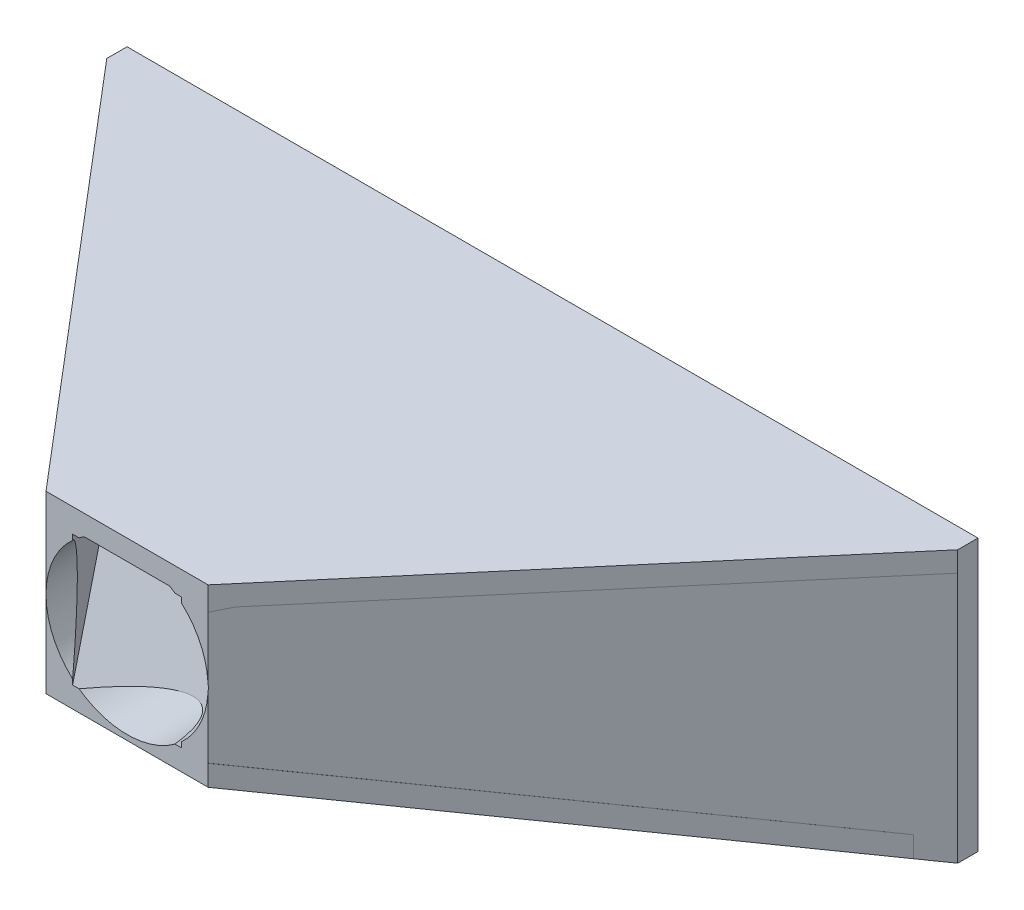
SolidWorks part; units mm, degrees
ref_plane "Plan de face" through (0, 0, 0) normal (0, 0, 1) x (1, 0, 0)
ref_plane "Plan de dessus" through (0, 0, 0) normal (0, 1, 0) x (1, 0, 0)
ref_plane "Plan de droite" through (0, 0, 0) normal (1, 0, 0) x (0, 0, -1)
sketch "Esquisse1" plane through (0, 0, 0) normal (0, 0, 1) x (1, 0, 0)
  line L0 (-5, 18.1802) -> (-5, -71.8198)
  line L1 (0, 13.1802) -> (200, 13.1802)
  line L2 (0, 13.1802) -> (0, -66.8198)
  line L3 (0, -66.8198) -> (200, -66.8198)
  line L4 (200, 13.1802) -> (200, -66.8198)
  line L5 (-5, -71.8198) -> (205, -71.8198)
  line L6 (205, 18.1802) -> (205, -71.8198)
  line L7 (-5, 18.1802) -> (205, 18.1802)
  dimension "D1" = 200
  dimension "D2" = 80
  dimension "D3" = 5
extrude "Boss.-Extru.1" add sketch "Esquisse1" along normal blind 5
ref_plane "Plan1" through (0, 0, 105) normal (0, 0, 1) x (1, 0, 0)
sketch "Esquisse2" plane through (0, 0, 105) normal (0, 0, 1) x (1, 0, 0)
  line L0 (200, 13.1802) -> (0, -66.8198) construction
  circle A0 centre (100, -26.8198) radius 15
  circle A1 centre (100, -26.8198) radius 20
  dimension "D1" = 30
  dimension "D2" = 5
extrude "Boss.-Extru.2" add sketch "Esquisse2" along normal blind 5 separate body
sketch "Esquisse3" plane through (0, -71.8198, 0) normal (0, -1, 0) x (1, 0, 0)
  line L0 (-5, 5) -> (80, 105)
  line L1 (119.9546, 105) -> (205, 5)
  line L2 (1.5622, 5) -> (86.5622, 105)
  line L3 (80, 105) -> (86.5622, 105) construction
  line L4 (80, 106.7952) -> (80, 103.9851) construction
  line L5 (100, 0) -> (100, 141.8233) construction
  line L6 (198.4378, 5) -> (113.4378, 105)
  line L7 (205, 5) -> (120, 105)
  line L8 (80, 105) -> (86.5622, 105)
  line L9 (113.4378, 105) -> (120, 105)
  line L10 (205, 5) -> (198.4378, 5)
  line L11 (-5, 5) -> (1.5622, 5)
  line M12 (205, 5) -> (-5, 5)
  dimension "D1" = 5
extrude "Boss.-Extru.3" add sketch "Esquisse3" against normal blind 90 contours L9 L6 L1 M12 | L8 L0 L2 M12
sketch "Esquisse5" plane through (200, 0, 0) normal (-1, 0, 0) x (0, 0, 1)
  line L0 (5, 18.1802) -> (105, -5.5548)
  line L1 (5, 13.0413) -> (105, -10.6937)
  line L2 (105, -5.5548) -> (105, -10.6937)
  line L3 (5, 18.1802) -> (5, 13.0413)
  line L4 (105, -46.8198) -> (105, -6.8198) construction
  line L5 (5, 18.1802) -> (5, -71.8198) construction
  line L6 (110, -26.8198) -> (-15.748, -26.8198) construction
  line L7 (5, -71.8198) -> (105, -48.0848)
  line L8 (105, -48.0848) -> (105, -42.9459)
  line L9 (5, -66.6809) -> (105, -42.9459)
  line L10 (5, -71.8198) -> (5, -66.6809)
  dimension "D1" = 5
extrude "Boss.-Extru.4" add sketch "Esquisse5" along normal blind 200
sketch "Esquisse6" plane through (0, 0, 105) normal (0, 0, -1) x (-1, 0, 0)
  line L1 (-113.4378, -10.6937) -> (-86.5622, -10.6937)
  line L2 (-113.4378, -10.6937) -> (-113.4378, -42.9459)
  line L3 (-113.4378, -42.9459) -> (-86.5622, -42.9459)
  line L4 (-86.5622, -10.6937) -> (-86.5622, -42.9459)
extrude "Enlèv. mat.-Extru.1" cut sketch "Esquisse6" against normal blind 200
sketch "Esquisse8" plane through (0, -71.8198, 0) normal (0, -1, 0) x (1, 0, 0)
  line L0 (0, 105) -> (80, 105)
  line L1 (80, 105) -> (0, 10.8824)
  line L2 (0, 10.8824) -> (0, 105)
  line L3 (100, 105) -> (100, -6.8293) construction
  line L4 (120, 105) -> (200, 10.8824)
  line L5 (200, 105) -> (120, 105)
  line L6 (200, 10.8824) -> (200, 105)
extrude "Enlèv. mat.-Extru.2" cut sketch "Esquisse8" against normal blind 200
sketch "Esquisse9" plane through (-5, 0, 0) normal (-1, 0, 0) x (0, 0, 1)
  line L0 (105, 18.1802) -> (105, -5.5548) construction
  line L1 (105, -5.5548) -> (5, 18.1802) construction
  line L2 (5, 18.1802) -> (105, 18.1802) construction
  line L3 (105, 18.1802) -> (105, -5.5548)
  line L4 (105, -5.5548) -> (5, 18.1802)
  line L5 (5, 18.1802) -> (105, 18.1802)
  line L6 (105, -26.8198) -> (-8.1644, -26.8198) construction
  line L7 (5, -71.8198) -> (105, -71.8198)
  line L8 (105, -48.0848) -> (5, -71.8198)
  line L9 (105, -71.8198) -> (105, -48.0848)
extrude "Enlèv. mat.-Extru.3" cut sketch "Esquisse9" against normal blind 237
sketch "Esquisse10" plane through (0, 0, 105) normal (0, 0, 1) x (1, 0, 0)
  circle A0 centre (100, -26.8198) radius 20 construction
  circle A1 centre (100, -26.8198) radius 20
extrude "Enlèv. mat.-Extru.4" cut sketch "Esquisse10" against normal through all both and the other way through all
ref_plane "Plan2" through (0, 13.1802, 0) normal (0, -1, 0) x (-1, 0, 0)
sketch "Esquisse11" plane through (0, 13.1802, 0) normal (0, -1, 0) x (-1, 0, 0)
  line L1 (-246.4324, 39.1361) -> (47.9527, 39.1361)
  line L2 (-246.4324, 39.1361) -> (-246.4324, -121.1294)
  line L3 (-246.4324, -121.1294) -> (47.9527, -121.1294)
  line L4 (47.9527, 39.1361) -> (47.9527, -121.1294)
extrude "Enlèv. mat.-Extru.5" cut sketch "Esquisse11" against normal blind 16 and the other way blind 23
sketch "Esquisse12" plane through (0, -9.8198, 0) normal (0, 1, 0) x (1, 0, 0)
  line L0 (-5, -5) -> (-5, 0)
  line L1 (-5, 0) -> (205, 0)
  line L2 (205, 0) -> (205, -5)
  line L3 (205, -5) -> (120, -105)
  line L4 (120, -105) -> (80, -105)
  line L5 (80, -105) -> (-5, -5)
extrude "Boss.-Extru.5" add sketch "Esquisse12" along normal blind 5
